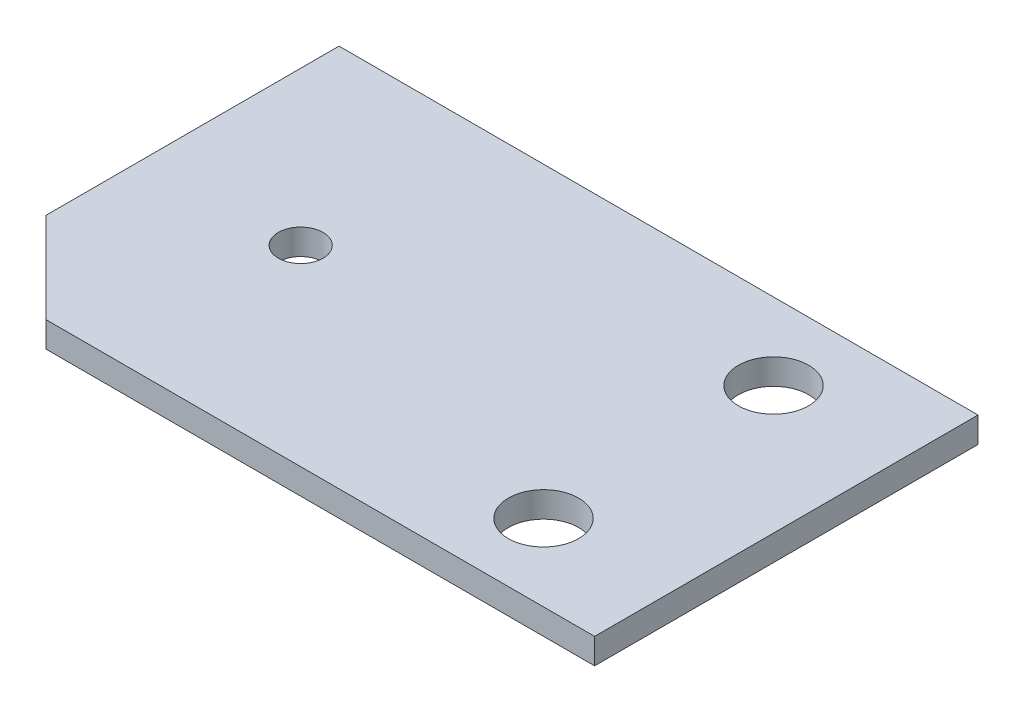
SolidWorks part; units mm, degrees
ref_plane "前视基准面" through (0, 0, 0) normal (0, 0, 1) x (1, 0, 0)
ref_plane "上视基准面" through (0, 0, 0) normal (0, 1, 0) x (1, 0, 0)
ref_plane "右视基准面" through (0, 0, 0) normal (1, 0, 0) x (0, 0, -1)
sketch "草图1" plane through (0, 0, 0) normal (0, 1, 0) x (1, 0, 0)
  line L0 (0, 0) -> (50, 0)
  line L1 (50, 0) -> (50, 30)
  line L2 (50, 30) -> (0, 30)
  line L3 (0, 30) -> (0, 0)
  dimension "D1" = 30
  dimension "D2" = 50
extrude "凸台-拉伸1" add sketch "草图1" along normal blind 2
sketch "草图2" plane through (0, 2, 0) normal (0, 1, 0) x (1, 0, 0)
  line L0 (50, 0) -> (50, 30) construction
  line L1 (0, 0) -> (50, 0) construction
  line L2 (0, 30) -> (0, 0) construction
  line L3 (0, 7.0711) -> (7.0711, 0)
  line L4 (0, 0) -> (0, 7.0711)
  line L5 (0, 0) -> (7.0711, 0)
  circle A0 centre (40, 6) radius 2.75
  circle A1 centre (12, 15) radius 1.75
  circle A2 centre (40, 24) radius 2.75
  dimension "D1" = 3.5
  dimension "D2" = 5.5
  dimension "D3" = 10
  dimension "D4" = 6
  dimension "D5" = 15
  dimension "D6" = 12
  dimension "D7" = 45
  dimension "D8" = 10
  dimension "D9" = 2
extrude "切除-拉伸1" cut sketch "草图2" against normal through all
